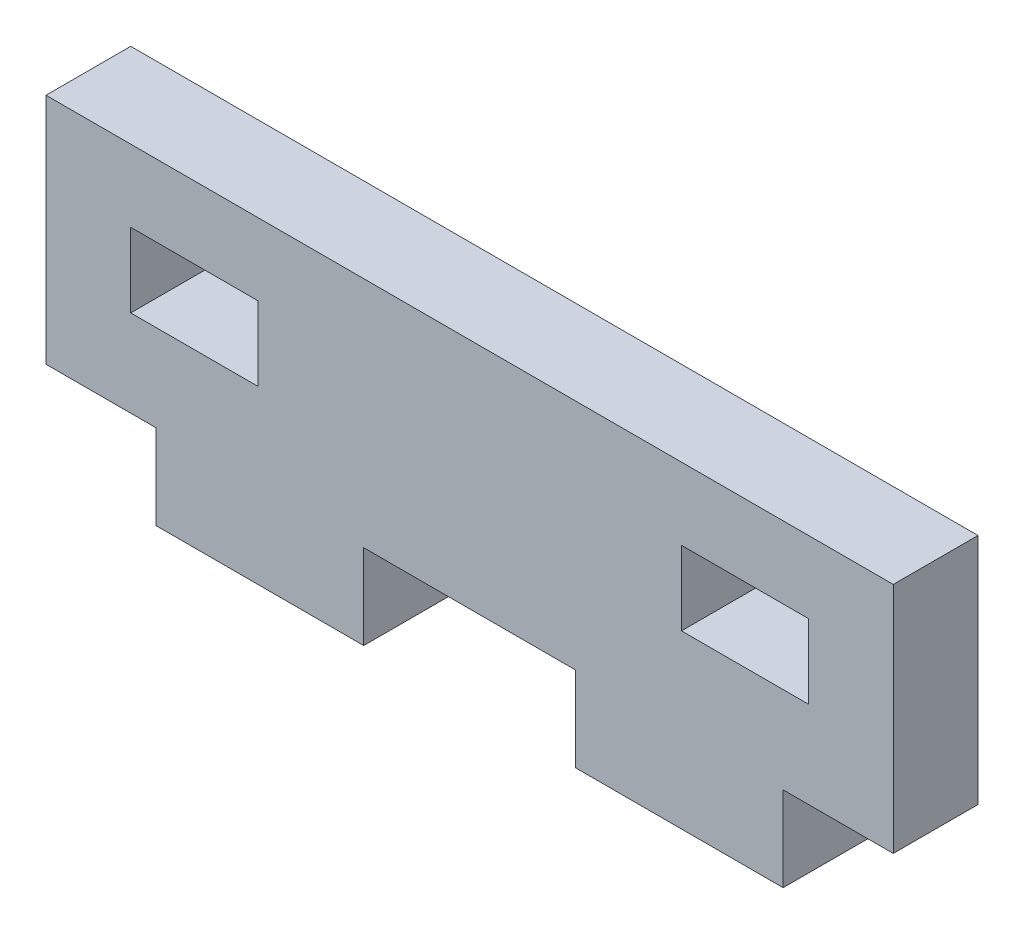
SolidWorks part; units mm, degrees
ref_plane "Ebene vorne" through (0, 0, 0) normal (0, 0, 1) x (1, 0, 0)
ref_plane "Ebene oben" through (0, 0, 0) normal (0, 1, 0) x (1, 0, 0)
ref_plane "Ebene rechts" through (0, 0, 0) normal (1, 0, 0) x (0, 0, -1)
sketch "Skizze2" plane through (0, 0, 0) normal (0, 0, 1) x (1, 0, 0)
  line L0 (0, 0) -> (0, 4)
  line L1 (0, 4) -> (-2.5, 4)
  line L2 (-2.5, 4) -> (-2.5, 15)
  line L3 (-2.5, 15) -> (37.5, 15)
  line L4 (37.5, 15) -> (37.5, 4)
  line L5 (37.5, 4) -> (35, 4)
  line L6 (35, 4) -> (35, 0)
  line L7 (35, 0) -> (0, 0)
  dimension "D1" = 4
  dimension "D2" = 40
  dimension "D3" = 35
  dimension "D4" = 15
extrude "Aufsatz-Linear austragen1" add sketch "Skizze2" along normal blind 4
sketch "Skizze3" plane through (0, 0, 4) normal (0, 0, 1) x (1, 0, 0)
  line L5 (17.5, 15.2219) -> (17.5, -7.258) construction
  line L10 (35, 0) -> (35, 4) construction
  line L11 (0, 4) -> (0, 0) construction
  line L12 (0, 0) -> (35, 0) construction
  line L13 (0, 4) -> (2.7, 4)
  line L14 (0, 4) -> (0, 0)
  line L15 (0, 0) -> (2.7, 0)
  line L16 (2.7, 4) -> (2.7, 0)
  line L17 (35, 4) -> (37.5, 4) construction
  line L18 (12.5, 4) -> (22.5, 4)
  line L19 (12.5, 4) -> (12.5, 0)
  line L20 (12.5, 0) -> (22.5, 0)
  line L21 (22.5, 4) -> (22.5, 0)
  line L22 (32.3, 0) -> (35, 0)
  line L23 (32.3, 0) -> (32.3, 4)
  line L24 (32.3, 4) -> (35, 4)
  line L25 (35, 0) -> (35, 4)
  dimension "D1" = 9.8
  dimension "D2" = 10
extrude "Schnitt-Linear austragen1" cut sketch "Skizze3" against normal up to next
sketch "Skizze4" plane through (0, 0, 4) normal (0, 0, 1) x (1, 0, 0)
  line L0 (17.5, 19.2491) -> (17.5, -7.8709) construction
  line L1 (1.5, 11.6) -> (7.5, 11.6)
  line L2 (1.5, 11.6) -> (1.5, 8.1)
  line L3 (1.5, 8.1) -> (7.5, 8.1)
  line L4 (7.5, 11.6) -> (7.5, 8.1)
  line L5 (37.5, 4) -> (37.5, 15) construction
  line L6 (-2.5, 15) -> (-2.5, 4) construction
  line L7 (-2.5, 4) -> (2.7, 4) construction
  line L8 (27.5, 8.1) -> (33.5, 8.1)
  line L9 (27.5, 8.1) -> (27.5, 11.6)
  line L10 (27.5, 11.6) -> (33.5, 11.6)
  line L11 (33.5, 8.1) -> (33.5, 11.6)
  point P14 (23.1707, 11.6731)
  dimension "D1" = 3.5
  dimension "D2" = 20
  dimension "D3" = 4.1
  dimension "D4" = 6
extrude "Schnitt-Linear austragen2" cut sketch "Skizze4" against normal up to next
